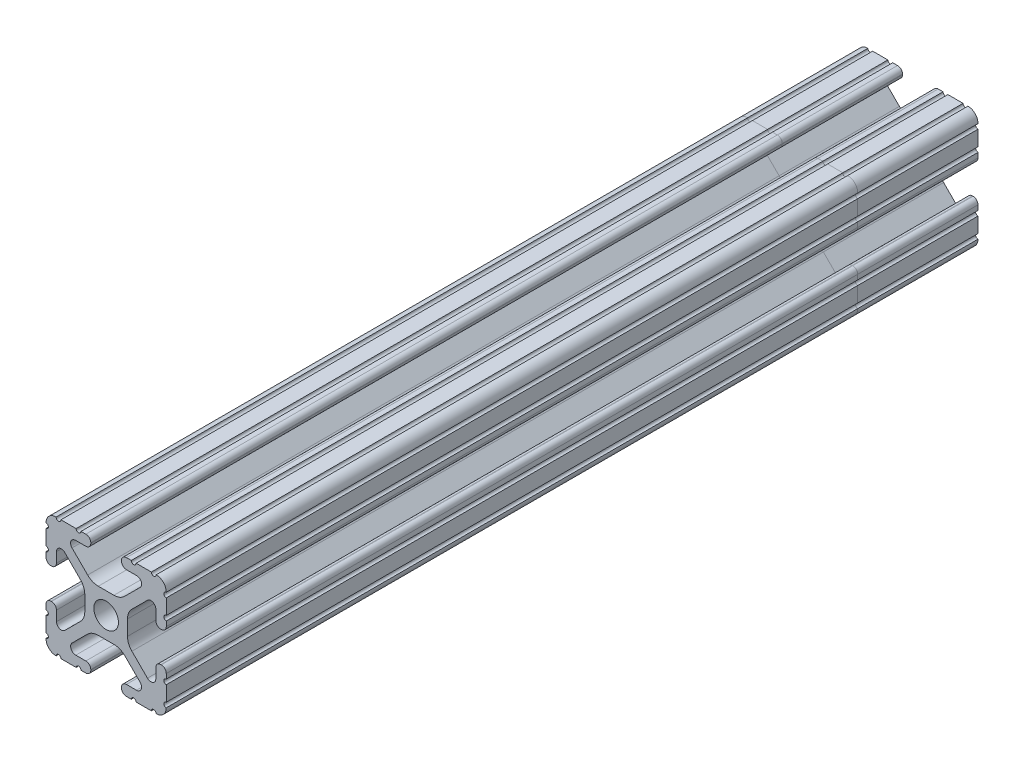
SolidWorks part; units mm, degrees
ref_plane "Front Plane" through (0, 0, 0) normal (0, 0, 1) x (1, 0, 0)
ref_plane "Top Plane" through (0, 0, 0) normal (0, 1, 0) x (1, 0, 0)
ref_plane "Right Plane" through (0, 0, 0) normal (1, 0, 0) x (0, 0, -1)
sketch "Sketch1" plane through (0, 0, 0) normal (0, 0, 1) x (1, 0, 0)
  line L88 (-7.1797, -8.6452) -> (-3.9523, -5.4237)
  line L89 (-1.7093, -4.4958) -> (1.7093, -4.4958)
  line L90 (3.9523, -5.4237) -> (7.1797, -8.6452)
  line L91 (6.4164, -10.4902) -> (4.2875, -10.4902)
  line L92 (3.2385, -11.5392) -> (3.2385, -11.651)
  line L93 (4.2875, -12.7) -> (5.3171, -12.7)
  line L94 (6.3331, -12.7) -> (9.5504, -12.7)
  line L95 (12.7, -9.5504) -> (12.7, -6.3331)
  line L96 (12.7, -5.3171) -> (12.7, -4.2875)
  line L97 (11.651, -3.2385) -> (11.5392, -3.2385)
  line L98 (10.4902, -4.2875) -> (10.4902, -6.4021)
  line L99 (8.7371, -7.1294) -> (5.441, -3.8408)
  line L100 (4.5085, -1.5932) -> (4.5085, 1.5932)
  line L101 (5.441, 3.8408) -> (8.7371, 7.1294)
  line L102 (10.4902, 6.4021) -> (10.4902, 4.2875)
  line L103 (11.5392, 3.2385) -> (11.651, 3.2385)
  line L104 (12.7, 4.2875) -> (12.7, 5.3171)
  line L105 (12.7, 6.3331) -> (12.7, 9.5504)
  line L106 (9.5504, 12.7) -> (6.3331, 12.7)
  line L107 (5.3171, 12.7) -> (4.2875, 12.7)
  line L108 (3.2385, 11.651) -> (3.2385, 11.5392)
  line L109 (4.2875, 10.4902) -> (6.4768, 10.4902)
  line L110 (7.207, 8.7244) -> (3.8983, 5.4232)
  line L111 (1.6558, 4.4958) -> (-1.6558, 4.4958)
  line L112 (-3.8983, 5.4232) -> (-7.207, 8.7244)
  line L113 (-6.4768, 10.4902) -> (-4.2875, 10.4902)
  line L114 (-3.2385, 11.5392) -> (-3.2385, 11.651)
  line L115 (-4.2875, 12.7) -> (-5.3171, 12.7)
  line L116 (-6.3331, 12.7) -> (-9.5504, 12.7)
  line L117 (-12.7, 9.5504) -> (-12.7, 6.3331)
  line L118 (-12.7, 5.3171) -> (-12.7, 4.2875)
  line L119 (-11.651, 3.2385) -> (-11.5392, 3.2385)
  line L120 (-10.4902, 4.2875) -> (-10.4902, 6.4021)
  line L121 (-8.7371, 7.1294) -> (-5.441, 3.8408)
  line L122 (-4.5085, 1.5932) -> (-4.5085, -1.5932)
  line L123 (-5.441, -3.8408) -> (-8.7371, -7.1294)
  line L124 (-10.4902, -6.4021) -> (-10.4902, -4.2875)
  line L125 (-11.5392, -3.2385) -> (-11.651, -3.2385)
  line L126 (-12.7, -4.2875) -> (-12.7, -5.3171)
  line L127 (-12.7, -6.3331) -> (-12.7, -9.5504)
  line L128 (-9.5504, -12.7) -> (-6.3331, -12.7)
  line L129 (-5.3171, -12.7) -> (-4.2875, -12.7)
  line L130 (-3.2385, -11.651) -> (-3.2385, -11.5392)
  line L131 (-4.2875, -10.4902) -> (-6.4164, -10.4902)
  circle A1 centre (0, 0) radius 2.6035
  arc A104 (-7.1797, -8.6452) -> (-6.4164, -10.4902) centre (-6.4164, -9.4098) ccw
  arc A105 (-1.7093, -4.4958) -> (-3.9523, -5.4237) centre (-1.7093, -7.6708) ccw
  arc A106 (3.9523, -5.4237) -> (1.7093, -4.4958) centre (1.7093, -7.6708) ccw
  arc A107 (6.4164, -10.4902) -> (7.1797, -8.6452) centre (6.4164, -9.4098) ccw
  arc A108 (4.2875, -10.4902) -> (3.2385, -11.5392) centre (4.2875, -11.5392) ccw
  arc A109 (3.2385, -11.651) -> (4.2875, -12.7) centre (4.2875, -11.651) ccw
  arc A110 (6.3331, -12.7) -> (5.3171, -12.7) centre (5.8251, -12.7) ccw
  arc A111 (10.5664, -12.6998) -> (9.5504, -12.7) centre (10.0584, -12.7) ccw
  arc A112 (10.5664, -12.6998) -> (12.6998, -10.5664) centre (10.5918, -10.5918) ccw
  arc A113 (12.7, -9.5504) -> (12.6998, -10.5664) centre (12.7, -10.0584) ccw
  arc A114 (12.7, -5.3171) -> (12.7, -6.3331) centre (12.7, -5.8251) ccw
  arc A115 (12.7, -4.2875) -> (11.651, -3.2385) centre (11.651, -4.2875) ccw
  arc A116 (11.5392, -3.2385) -> (10.4902, -4.2875) centre (11.5392, -4.2875) ccw
  arc A117 (8.7371, -7.1294) -> (10.4902, -6.4021) centre (9.4628, -6.4021) ccw
  arc A118 (4.5085, -1.5932) -> (5.441, -3.8408) centre (7.6835, -1.5932) ccw
  arc A119 (5.441, 3.8408) -> (4.5085, 1.5932) centre (7.6835, 1.5932) ccw
  arc A120 (10.4902, 6.4021) -> (8.7371, 7.1294) centre (9.4628, 6.4021) ccw
  arc A121 (10.4902, 4.2875) -> (11.5392, 3.2385) centre (11.5392, 4.2875) ccw
  arc A122 (11.651, 3.2385) -> (12.7, 4.2875) centre (11.651, 4.2875) ccw
  arc A123 (12.7, 6.3331) -> (12.7, 5.3171) centre (12.7, 5.8251) ccw
  arc A124 (12.6998, 10.5664) -> (12.7, 9.5504) centre (12.7, 10.0584) ccw
  arc A125 (12.6998, 10.5664) -> (10.5664, 12.6998) centre (10.5918, 10.5918) ccw
  arc A126 (9.5504, 12.7) -> (10.5664, 12.6998) centre (10.0584, 12.7) ccw
  arc A127 (5.3171, 12.7) -> (6.3331, 12.7) centre (5.8251, 12.7) ccw
  arc A128 (4.2875, 12.7) -> (3.2385, 11.651) centre (4.2875, 11.651) ccw
  arc A129 (3.2385, 11.5392) -> (4.2875, 10.4902) centre (4.2875, 11.5392) ccw
  arc A130 (7.207, 8.7244) -> (6.4768, 10.4902) centre (6.4768, 9.4563) ccw
  arc A131 (1.6558, 4.4958) -> (3.8983, 5.4232) centre (1.6558, 7.6708) ccw
  arc A132 (-3.8983, 5.4232) -> (-1.6558, 4.4958) centre (-1.6558, 7.6708) ccw
  arc A133 (-6.4768, 10.4902) -> (-7.207, 8.7244) centre (-6.4768, 9.4563) ccw
  arc A134 (-4.2875, 10.4902) -> (-3.2385, 11.5392) centre (-4.2875, 11.5392) ccw
  arc A135 (-3.2385, 11.651) -> (-4.2875, 12.7) centre (-4.2875, 11.651) ccw
  arc A136 (-6.3331, 12.7) -> (-5.3171, 12.7) centre (-5.8251, 12.7) ccw
  arc A137 (-10.5664, 12.6998) -> (-9.5504, 12.7) centre (-10.0584, 12.7) ccw
  arc A138 (-10.5664, 12.6998) -> (-12.6998, 10.5664) centre (-10.5918, 10.5918) ccw
  arc A139 (-12.7, 9.5504) -> (-12.6998, 10.5664) centre (-12.7, 10.0584) ccw
  arc A140 (-12.7, 5.3171) -> (-12.7, 6.3331) centre (-12.7, 5.8251) ccw
  arc A141 (-12.7, 4.2875) -> (-11.651, 3.2385) centre (-11.651, 4.2875) ccw
  arc A142 (-11.5392, 3.2385) -> (-10.4902, 4.2875) centre (-11.5392, 4.2875) ccw
  arc A143 (-8.7371, 7.1294) -> (-10.4902, 6.4021) centre (-9.4628, 6.4021) ccw
  arc A144 (-4.5085, 1.5932) -> (-5.441, 3.8408) centre (-7.6835, 1.5932) ccw
  arc A145 (-5.441, -3.8408) -> (-4.5085, -1.5932) centre (-7.6835, -1.5932) ccw
  arc A146 (-10.4902, -6.4021) -> (-8.7371, -7.1294) centre (-9.4628, -6.4021) ccw
  arc A147 (-10.4902, -4.2875) -> (-11.5392, -3.2385) centre (-11.5392, -4.2875) ccw
  arc A148 (-11.651, -3.2385) -> (-12.7, -4.2875) centre (-11.651, -4.2875) ccw
  arc A149 (-12.7, -6.3331) -> (-12.7, -5.3171) centre (-12.7, -5.8251) ccw
  arc A150 (-12.6998, -10.5664) -> (-12.7, -9.5504) centre (-12.7, -10.0584) ccw
  arc A151 (-12.6998, -10.5664) -> (-10.5664, -12.6998) centre (-10.5918, -10.5918) ccw
  arc A152 (-9.5504, -12.7) -> (-10.5664, -12.6998) centre (-10.0584, -12.7) ccw
  arc A153 (-5.3171, -12.7) -> (-6.3331, -12.7) centre (-5.8251, -12.7) ccw
  arc A154 (-4.2875, -12.7) -> (-3.2385, -11.651) centre (-4.2875, -11.651) ccw
  arc A155 (-3.2385, -11.5392) -> (-4.2875, -10.4902) centre (-4.2875, -11.5392) ccw
extrude "Boss-Extrude1" add sketch "Sketch1" along normal mid plane 171.45
ref_plane "Plane1" through (0, 0, -60.325) normal (0, 0, -1) x (-1, 0, 0)
split "Split1" trim tools "Plane1" bodies to split 103 resulting bodies 105 106
